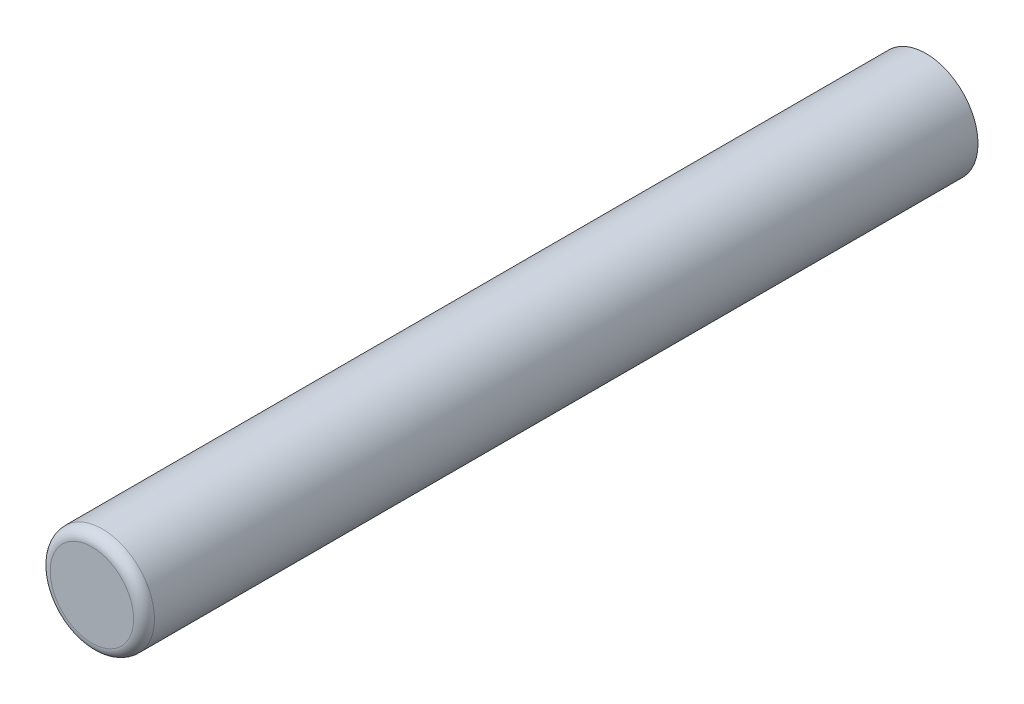
SolidWorks part; units mm, degrees
material "6061-T6 (SS)"
ref_plane "Front Plane" through (0, 0, 0) normal (0, 0, 1) x (1, 0, 0)
ref_plane "Top Plane" through (0, 0, 0) normal (0, 1, 0) x (1, 0, 0)
ref_plane "Right Plane" through (0, 0, 0) normal (1, 0, 0) x (0, 0, -1)
sketch "Sketch1" plane through (0, 0, 0) normal (0, 0, 1) x (1, 0, 0)
  circle A0 centre (0, 0) radius 6.35
  dimension "D1" = 12.7
extrude "Boss-Extrude1" add sketch "Sketch1" along normal blind 101.6
sketch "Sketch2" plane through (0, 0, 0) normal (0, 0, -1) x (-1, 0, 0)
  point P0 (0, 0)
hole_wizard "M5x0.8 Tapped Hole1" positions "Sketch3" profile "Sketch4" tap size "M5x0.8" standard "ANSI Metric"
sketch "Sketch3" plane through (0, 0, 0) normal (0, 0, -1) x (-1, 0, 0)
  point P0 (0, 0)
sketch "Sketch4" plane through (0, 0, 0) normal (1, 0, 0) x (0, 1, 0)
  line L0 (0, 0) -> (0, 26.6618)
  line L1 (0, 26.6618) -> (2.1, 25.4)
  line L2 (2.1, 25.4) -> (2.1, 0)
  line L5 (2.1, 0) -> (0, 0)
  line L10 (0, 26.6618) -> (-2.1, 25.4) construction
  line L11 (0, -6.35) -> (0, 107.95) construction
  dimension "Tap Drill Dia." = 4.2
  dimension "Tap Drill Depth" = 25.4
  dimension "Drill Angle" = 118
cosmetic thread "Hole Thread1"
fillet "Fillet1" radius 1.27 1 edges at (6.35, 0, 101.6)
